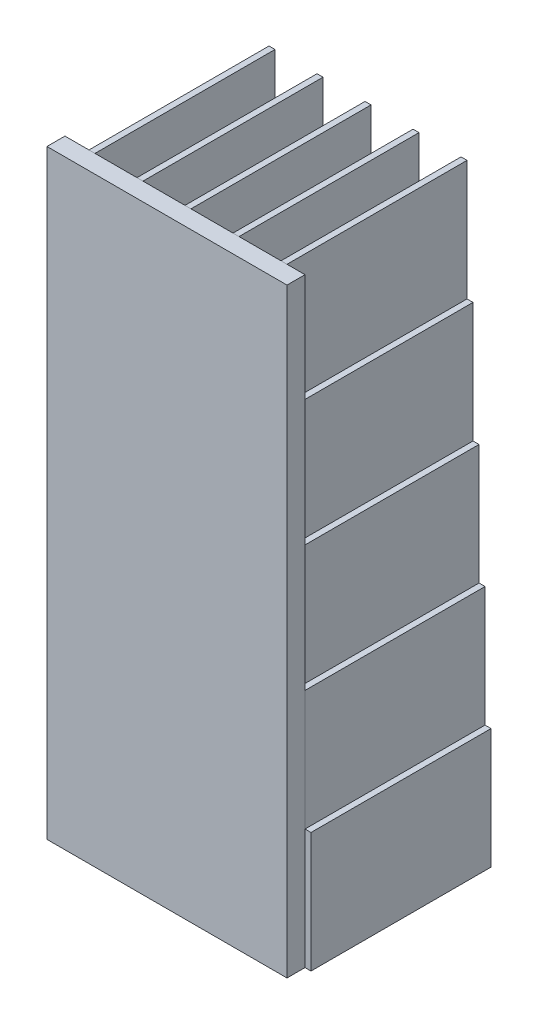
SolidWorks part; units mm, degrees
ref_plane "Front Plane" through (0, 0, 0) normal (0, 0, 1) x (1, 0, 0)
ref_plane "Top Plane" through (0, 0, 0) normal (0, 1, 0) x (1, 0, 0)
ref_plane "Right Plane" through (0, 0, 0) normal (1, 0, 0) x (0, 0, -1)
sketch "Sketch1" plane through (0, 0, 0) normal (0, 0, 1) x (1, 0, 0)
  line L361 (-45.534, 24.8846) -> (-44.534, 24.8846)
  line L362 (-46.534, 24.8846) -> (-45.534, 24.8846)
  line L363 (-46.534, 24.8846) -> (-46.534, 4.8846)
  line L364 (-46.534, 4.8846) -> (-45.534, 4.8846)
  line L365 (-45.534, 24.8846) -> (-45.534, 4.8846)
  line L366 (-45.534, 24.8846) -> (-44.534, 24.8846)
  line L367 (-45.534, 24.8846) -> (-45.534, 44.8846)
  line L368 (-45.534, 44.8846) -> (-44.534, 44.8846)
  line L369 (-44.534, 24.8846) -> (-44.534, 44.8846)
  line L371 (-44.534, 24.8846) -> (-44.534, 44.8846)
  line L372 (-44.534, 44.8846) -> (-43.534, 44.8846)
  line L374 (-38.534, 24.8846) -> (-37.534, 24.8846)
  line L379 (-38.534, 24.8846) -> (-38.534, 4.8846)
  line L384 (-38.534, 4.8846) -> (-37.534, 4.8846)
  line L389 (-37.534, 24.8846) -> (-37.534, 4.8846)
  line L392 (-40.534, 44.8846) -> (-39.534, 44.8846)
  line L393 (-39.534, 24.8846) -> (-39.534, 44.8846)
  line L394 (-37.534, 24.8846) -> (-36.534, 24.8846)
  line L395 (-39.534, 24.8846) -> (-38.534, 24.8846)
  line L396 (-39.534, 24.8846) -> (-39.534, 44.8846)
  line L397 (-39.534, 44.8846) -> (-38.534, 44.8846)
  line L398 (-38.534, 24.8846) -> (-38.534, 44.8846)
  line L399 (-45.534, 44.8846) -> (-44.534, 44.8846)
  line L400 (-45.534, 44.8846) -> (-44.534, 44.8846)
  line L403 (-44.534, 44.8846) -> (-44.534, 64.8846)
  line L404 (-44.534, 44.8846) -> (-43.534, 44.8846)
  line L405 (-44.534, 44.8846) -> (-44.534, 64.8846)
  line L406 (-44.534, 64.8846) -> (-43.534, 64.8846)
  line L407 (-43.534, 44.8846) -> (-43.534, 64.8846)
  line L408 (-44.534, 44.8846) -> (-43.534, 44.8846)
  line L410 (-43.534, 44.8846) -> (-43.534, 64.8846)
  line L411 (-43.534, 64.8846) -> (-42.534, 64.8846)
  line L413 (-37.534, 24.8846) -> (-36.534, 24.8846)
  line L418 (-37.534, 24.8846) -> (-37.534, 44.8846)
  line L421 (-41.534, 64.8846) -> (-40.534, 64.8846)
  line L422 (-40.534, 44.8846) -> (-40.534, 64.8846)
  line L423 (-37.534, 44.8846) -> (-36.534, 44.8846)
  line L424 (-40.534, 44.8846) -> (-39.534, 44.8846)
  line L425 (-40.534, 44.8846) -> (-40.534, 64.8846)
  line L426 (-40.534, 64.8846) -> (-39.534, 64.8846)
  line L427 (-39.534, 44.8846) -> (-39.534, 64.8846)
  line L428 (-40.534, 44.8846) -> (-39.534, 44.8846)
  line L429 (-39.534, 44.8846) -> (-38.534, 44.8846)
  line L430 (-39.534, 44.8846) -> (-39.534, 64.8846)
  line L433 (-36.534, 24.8846) -> (-36.534, 44.8846)
  line L438 (-44.534, 64.8846) -> (-43.534, 64.8846)
  line L441 (-43.534, 64.8846) -> (-43.534, 84.8846)
  line L442 (-44.534, 64.8846) -> (-43.534, 64.8846)
  line L443 (-43.534, 64.8846) -> (-42.534, 64.8846)
  line L444 (-43.534, 64.8846) -> (-43.534, 84.8846)
  line L445 (-43.534, 84.8846) -> (-42.534, 84.8846)
  line L446 (-42.534, 64.8846) -> (-42.534, 84.8846)
  line L447 (-43.534, 64.8846) -> (-42.534, 64.8846)
  line L449 (-42.534, 64.8846) -> (-42.534, 84.8846)
  line L450 (-42.534, 84.8846) -> (-41.534, 84.8846)
  line L451 (-41.534, 64.8846) -> (-41.534, 84.8846)
  line L452 (-36.534, 24.8846) -> (-36.534, 44.8846)
  line L453 (-41.534, 64.8846) -> (-40.534, 64.8846)
  line L454 (-41.534, 64.8846) -> (-41.534, 84.8846)
  line L455 (-41.534, 84.8846) -> (-40.534, 84.8846)
  line L456 (-40.534, 64.8846) -> (-40.534, 84.8846)
  line L457 (-41.534, 64.8846) -> (-40.534, 64.8846)
  line L458 (-40.534, 64.8846) -> (-39.534, 64.8846)
  line L459 (-40.534, 64.8846) -> (-40.534, 84.8846)
  line L462 (-40.534, 64.8846) -> (-39.534, 64.8846)
  line L467 (-36.534, 44.8846) -> (-35.534, 44.8846)
  line L476 (-32.534, 44.8846) -> (-31.534, 44.8846)
  line L477 (-43.534, 84.8846) -> (-42.534, 84.8846)
  line L480 (-42.534, 84.8846) -> (-42.534, 104.8846)
  line L481 (-43.534, 84.8846) -> (-42.534, 84.8846)
  line L482 (-42.534, 84.8846) -> (-41.534, 84.8846)
  line L483 (-42.534, 84.8846) -> (-42.534, 104.8846)
  line L484 (-42.534, 104.8846) -> (-41.534, 104.8846)
  line L485 (-41.534, 84.8846) -> (-41.534, 104.8846)
  line L486 (-42.534, 84.8846) -> (-41.534, 84.8846)
  line L487 (-41.534, 84.8846) -> (-40.534, 84.8846)
  line L488 (-41.534, 84.8846) -> (-41.534, 104.8846)
  line L491 (-41.534, 84.8846) -> (-40.534, 84.8846)
  line L496 (-31.534, 24.8846) -> (-31.534, 44.8846)
  line L501 (-44.534, 24.8846) -> (-43.534, 24.8846) [skipped]
  line L502 (-44.534, 24.8846) -> (-43.534, 24.8846) [skipped]
  line L503 (-43.534, 24.8846) -> (-43.534, 44.8846) [skipped]
  line L504 (-43.534, 24.8846) -> (-43.534, 44.8846) [skipped]
  line L505 (-42.534, 24.8846) -> (-42.534, 44.8846) [skipped]
  line L506 (-42.534, 24.8846) -> (-42.534, 44.8846) [skipped]
  line L507 (-41.534, 24.8846) -> (-41.534, 44.8846) [skipped]
  line L508 (-41.534, 24.8846) -> (-41.534, 44.8846) [skipped]
  line L509 (-40.534, 24.8846) -> (-40.534, 44.8846) [skipped]
  line L510 (-40.534, 24.8846) -> (-40.534, 44.8846) [skipped]
  line L511 (-40.534, 24.8846) -> (-39.534, 24.8846) [skipped]
  line L512 (-40.534, 24.8846) -> (-39.534, 24.8846) [skipped]
  line L513 (-41.534, 24.8846) -> (-40.534, 24.8846) [skipped]
  line L514 (-41.534, 24.8846) -> (-40.534, 24.8846) [skipped]
  line L515 (-42.534, 24.8846) -> (-41.534, 24.8846) [skipped]
  line L516 (-42.534, 24.8846) -> (-41.534, 24.8846) [skipped]
  line L517 (-43.534, 24.8846) -> (-42.534, 24.8846) [skipped]
  line L518 (-43.534, 24.8846) -> (-42.534, 24.8846) [skipped]
  line L519 (-43.534, 44.8846) -> (-42.534, 44.8846) [skipped]
  line L520 (-41.534, 44.8846) -> (-40.534, 44.8846) [skipped]
  line L521 (-42.534, 44.8846) -> (-41.534, 44.8846) [skipped]
  line L522 (-45.534, 44.8846) -> (-45.534, 64.8846) [skipped]
  line L523 (-38.534, 44.8846) -> (-38.534, 64.8846) [skipped]
  line L524 (-45.534, 64.8846) -> (-45.534, 84.8846) [skipped]
  line L525 (-44.534, 64.8846) -> (-44.534, 84.8846) [skipped]
  line L526 (-44.534, 64.8846) -> (-44.534, 84.8846) [skipped]
  line L527 (-45.534, 64.8846) -> (-44.534, 64.8846) [skipped]
  line L528 (-45.534, 64.8846) -> (-44.534, 64.8846) [skipped]
  line L529 (-45.534, 64.8846) -> (-44.534, 64.8846) [skipped]
  line L530 (-39.534, 64.8846) -> (-38.534, 64.8846) [skipped]
  line L531 (-39.534, 64.8846) -> (-38.534, 64.8846) [skipped]
  line L532 (-39.534, 64.8846) -> (-39.534, 84.8846) [skipped]
  line L533 (-39.534, 64.8846) -> (-39.534, 84.8846) [skipped]
  line L534 (-38.534, 64.8846) -> (-38.534, 84.8846) [skipped]
  line L535 (-45.534, 84.8846) -> (-45.534, 104.8846) [skipped]
  line L536 (-44.534, 84.8846) -> (-44.534, 104.8846) [skipped]
  line L537 (-44.534, 84.8846) -> (-44.534, 104.8846) [skipped]
  line L538 (-45.534, 84.8846) -> (-44.534, 84.8846) [skipped]
  line L539 (-45.534, 84.8846) -> (-44.534, 84.8846) [skipped]
  line L540 (-45.534, 84.8846) -> (-44.534, 84.8846) [skipped]
  line L541 (-44.534, 84.8846) -> (-43.534, 84.8846) [skipped]
  line L542 (-40.534, 84.8846) -> (-39.534, 84.8846) [skipped]
  line L543 (-39.534, 84.8846) -> (-39.534, 104.8846) [skipped]
  line L544 (-39.534, 84.8846) -> (-39.534, 104.8846) [skipped]
  line L545 (-39.534, 84.8846) -> (-38.534, 84.8846) [skipped]
  line L546 (-39.534, 84.8846) -> (-38.534, 84.8846) [skipped]
  line L547 (-38.534, 84.8846) -> (-38.534, 104.8846) [skipped]
  line L548 (-45.534, 104.8846) -> (-44.534, 104.8846) [skipped]
  line L549 (-44.534, 104.8846) -> (-43.534, 104.8846) [skipped]
  line L550 (-40.534, 104.8846) -> (-39.534, 104.8846) [skipped]
  line L551 (-39.534, 104.8846) -> (-38.534, 104.8846) [skipped]
  line L552 (-31.534, 24.8846) -> (-30.534, 24.8846)
  line L553 (-31.534, 24.8846) -> (-31.534, 44.8846)
  line L554 (-31.534, 44.8846) -> (-30.534, 44.8846)
  line L555 (-30.534, 24.8846) -> (-30.534, 44.8846)
  line L556 (-37.534, 44.8846) -> (-36.534, 44.8846)
  line L557 (-37.534, 44.8846) -> (-36.534, 44.8846)
  line L558 (-36.534, 44.8846) -> (-35.534, 44.8846)
  line L559 (-36.534, 44.8846) -> (-35.534, 44.8846)
  line L560 (-32.534, 44.8846) -> (-31.534, 44.8846)
  line L561 (-32.534, 44.8846) -> (-31.534, 44.8846)
  line L562 (-31.534, 44.8846) -> (-30.534, 44.8846)
  line L563 (-36.534, 44.8846) -> (-36.534, 64.8846)
  line L564 (-36.534, 44.8846) -> (-36.534, 64.8846)
  line L565 (-36.534, 64.8846) -> (-35.534, 64.8846)
  line L566 (-35.534, 44.8846) -> (-35.534, 64.8846)
  line L567 (-35.534, 44.8846) -> (-35.534, 64.8846)
  line L568 (-35.534, 64.8846) -> (-34.534, 64.8846)
  line L569 (-33.534, 64.8846) -> (-32.534, 64.8846)
  line L570 (-32.534, 44.8846) -> (-32.534, 64.8846)
  line L571 (-32.534, 44.8846) -> (-32.534, 64.8846)
  line L572 (-32.534, 64.8846) -> (-31.534, 64.8846)
  line L573 (-31.534, 44.8846) -> (-31.534, 64.8846)
  line L574 (-31.534, 44.8846) -> (-31.534, 64.8846)
  line L575 (-36.534, 64.8846) -> (-35.534, 64.8846)
  line L576 (-35.534, 64.8846) -> (-35.534, 84.8846)
  line L577 (-36.534, 64.8846) -> (-35.534, 64.8846)
  line L578 (-35.534, 64.8846) -> (-34.534, 64.8846)
  line L579 (-35.534, 64.8846) -> (-35.534, 84.8846)
  line L580 (-35.534, 84.8846) -> (-34.534, 84.8846)
  line L581 (-34.534, 64.8846) -> (-34.534, 84.8846)
  line L582 (-35.534, 64.8846) -> (-34.534, 64.8846)
  line L583 (-34.534, 64.8846) -> (-34.534, 84.8846)
  line L584 (-34.534, 84.8846) -> (-33.534, 84.8846)
  line L585 (-33.534, 64.8846) -> (-33.534, 84.8846)
  line L586 (-33.534, 64.8846) -> (-32.534, 64.8846)
  line L587 (-33.534, 64.8846) -> (-33.534, 84.8846)
  line L588 (-33.534, 84.8846) -> (-32.534, 84.8846)
  line L589 (-32.534, 64.8846) -> (-32.534, 84.8846)
  line L590 (-33.534, 64.8846) -> (-32.534, 64.8846)
  line L591 (-32.534, 64.8846) -> (-31.534, 64.8846)
  line L592 (-32.534, 64.8846) -> (-32.534, 84.8846)
  line L593 (-32.534, 64.8846) -> (-31.534, 64.8846)
  line L594 (-35.534, 84.8846) -> (-34.534, 84.8846)
  line L595 (-34.534, 84.8846) -> (-34.534, 104.8846)
  line L596 (-35.534, 84.8846) -> (-34.534, 84.8846)
  line L597 (-34.534, 84.8846) -> (-33.534, 84.8846)
  line L598 (-34.534, 84.8846) -> (-34.534, 104.8846)
  line L599 (-34.534, 104.8846) -> (-33.534, 104.8846)
  line L600 (-33.534, 84.8846) -> (-33.534, 104.8846)
  line L601 (-34.534, 84.8846) -> (-33.534, 84.8846)
  line L602 (-33.534, 84.8846) -> (-32.534, 84.8846)
  line L603 (-33.534, 84.8846) -> (-33.534, 104.8846)
  line L604 (-33.534, 84.8846) -> (-32.534, 84.8846)
  line L605 (-29.534, 24.8846) -> (-28.534, 24.8846)
  line L606 (-29.534, 24.8846) -> (-28.534, 24.8846)
  line L607 (-29.534, 24.8846) -> (-29.534, 44.8846)
  line L608 (-29.534, 44.8846) -> (-28.534, 44.8846)
  line L609 (-28.534, 24.8846) -> (-28.534, 44.8846)
  line L610 (-28.534, 24.8846) -> (-28.534, 44.8846)
  line L611 (-28.534, 44.8846) -> (-27.534, 44.8846)
  line L612 (-24.534, 44.8846) -> (-23.534, 44.8846)
  line L613 (-23.534, 24.8846) -> (-23.534, 44.8846)
  line L614 (-23.534, 24.8846) -> (-22.534, 24.8846)
  line L615 (-23.534, 24.8846) -> (-23.534, 44.8846)
  line L616 (-23.534, 44.8846) -> (-22.534, 44.8846)
  line L617 (-22.534, 24.8846) -> (-22.534, 44.8846)
  line L618 (-29.534, 44.8846) -> (-28.534, 44.8846)
  line L619 (-29.534, 44.8846) -> (-28.534, 44.8846)
  line L620 (-28.534, 44.8846) -> (-27.534, 44.8846)
  line L621 (-28.534, 44.8846) -> (-27.534, 44.8846)
  line L622 (-24.534, 44.8846) -> (-23.534, 44.8846)
  line L623 (-24.534, 44.8846) -> (-23.534, 44.8846)
  line L624 (-23.534, 44.8846) -> (-22.534, 44.8846)
  line L625 (-28.534, 44.8846) -> (-28.534, 64.8846)
  line L626 (-28.534, 44.8846) -> (-28.534, 64.8846)
  line L627 (-28.534, 64.8846) -> (-27.534, 64.8846)
  line L628 (-27.534, 44.8846) -> (-27.534, 64.8846)
  line L629 (-27.534, 44.8846) -> (-27.534, 64.8846)
  line L630 (-27.534, 64.8846) -> (-26.534, 64.8846)
  line L631 (-25.534, 64.8846) -> (-24.534, 64.8846)
  line L632 (-24.534, 44.8846) -> (-24.534, 64.8846)
  line L633 (-24.534, 44.8846) -> (-24.534, 64.8846)
  line L634 (-24.534, 64.8846) -> (-23.534, 64.8846)
  line L635 (-23.534, 44.8846) -> (-23.534, 64.8846)
  line L636 (-23.534, 44.8846) -> (-23.534, 64.8846)
  line L637 (-28.534, 64.8846) -> (-27.534, 64.8846)
  line L638 (-27.534, 64.8846) -> (-27.534, 84.8846)
  line L639 (-28.534, 64.8846) -> (-27.534, 64.8846)
  line L640 (-27.534, 64.8846) -> (-26.534, 64.8846)
  line L641 (-27.534, 64.8846) -> (-27.534, 84.8846)
  line L642 (-27.534, 84.8846) -> (-26.534, 84.8846)
  line L643 (-26.534, 64.8846) -> (-26.534, 84.8846)
  line L644 (-27.534, 64.8846) -> (-26.534, 64.8846)
  line L645 (-26.534, 64.8846) -> (-26.534, 84.8846)
  line L646 (-26.534, 84.8846) -> (-25.534, 84.8846)
  line L647 (-25.534, 64.8846) -> (-25.534, 84.8846)
  line L648 (-25.534, 64.8846) -> (-24.534, 64.8846)
  line L649 (-25.534, 64.8846) -> (-25.534, 84.8846)
  line L650 (-25.534, 84.8846) -> (-24.534, 84.8846)
  line L651 (-24.534, 64.8846) -> (-24.534, 84.8846)
  line L652 (-25.534, 64.8846) -> (-24.534, 64.8846)
  line L653 (-24.534, 64.8846) -> (-23.534, 64.8846)
  line L654 (-24.534, 64.8846) -> (-24.534, 84.8846)
  line L655 (-24.534, 64.8846) -> (-23.534, 64.8846)
  line L656 (-27.534, 84.8846) -> (-26.534, 84.8846)
  line L657 (-26.534, 84.8846) -> (-26.534, 104.8846)
  line L658 (-27.534, 84.8846) -> (-26.534, 84.8846)
  line L659 (-26.534, 84.8846) -> (-25.534, 84.8846)
  line L660 (-26.534, 84.8846) -> (-26.534, 104.8846)
  line L661 (-26.534, 104.8846) -> (-25.534, 104.8846)
  line L662 (-25.534, 84.8846) -> (-25.534, 104.8846)
  line L663 (-26.534, 84.8846) -> (-25.534, 84.8846)
  line L664 (-25.534, 84.8846) -> (-24.534, 84.8846)
  line L665 (-25.534, 84.8846) -> (-25.534, 104.8846)
  line L666 (-25.534, 84.8846) -> (-24.534, 84.8846)
  line L667 (-21.534, 24.8846) -> (-20.534, 24.8846)
  line L668 (-21.534, 24.8846) -> (-20.534, 24.8846)
  line L669 (-21.534, 24.8846) -> (-21.534, 44.8846)
  line L670 (-21.534, 44.8846) -> (-20.534, 44.8846)
  line L671 (-20.534, 24.8846) -> (-20.534, 44.8846)
  line L672 (-20.534, 24.8846) -> (-20.534, 44.8846)
  line L673 (-20.534, 44.8846) -> (-19.534, 44.8846)
  line L674 (-16.534, 44.8846) -> (-15.534, 44.8846)
  line L675 (-15.534, 24.8846) -> (-15.534, 44.8846)
  line L676 (-15.534, 24.8846) -> (-14.534, 24.8846)
  line L677 (-15.534, 24.8846) -> (-15.534, 44.8846)
  line L678 (-15.534, 44.8846) -> (-14.534, 44.8846)
  line L679 (-14.534, 24.8846) -> (-14.534, 44.8846)
  line L680 (-21.534, 44.8846) -> (-20.534, 44.8846)
  line L681 (-21.534, 44.8846) -> (-20.534, 44.8846)
  line L682 (-20.534, 44.8846) -> (-19.534, 44.8846)
  line L683 (-20.534, 44.8846) -> (-19.534, 44.8846)
  line L684 (-16.534, 44.8846) -> (-15.534, 44.8846)
  line L685 (-16.534, 44.8846) -> (-15.534, 44.8846)
  line L686 (-15.534, 44.8846) -> (-14.534, 44.8846)
  line L687 (-20.534, 44.8846) -> (-20.534, 64.8846)
  line L688 (-20.534, 44.8846) -> (-20.534, 64.8846)
  line L689 (-20.534, 64.8846) -> (-19.534, 64.8846)
  line L690 (-19.534, 44.8846) -> (-19.534, 64.8846)
  line L691 (-19.534, 44.8846) -> (-19.534, 64.8846)
  line L692 (-19.534, 64.8846) -> (-18.534, 64.8846)
  line L693 (-17.534, 64.8846) -> (-16.534, 64.8846)
  line L694 (-16.534, 44.8846) -> (-16.534, 64.8846)
  line L695 (-16.534, 44.8846) -> (-16.534, 64.8846)
  line L696 (-16.534, 64.8846) -> (-15.534, 64.8846)
  line L697 (-15.534, 44.8846) -> (-15.534, 64.8846)
  line L698 (-15.534, 44.8846) -> (-15.534, 64.8846)
  line L699 (-20.534, 64.8846) -> (-19.534, 64.8846)
  line L700 (-19.534, 64.8846) -> (-19.534, 84.8846)
  line L701 (-20.534, 64.8846) -> (-19.534, 64.8846)
  line L702 (-19.534, 64.8846) -> (-18.534, 64.8846)
  line L703 (-19.534, 64.8846) -> (-19.534, 84.8846)
  line L704 (-19.534, 84.8846) -> (-18.534, 84.8846)
  line L705 (-18.534, 64.8846) -> (-18.534, 84.8846)
  line L706 (-19.534, 64.8846) -> (-18.534, 64.8846)
  line L707 (-18.534, 64.8846) -> (-18.534, 84.8846)
  line L708 (-18.534, 84.8846) -> (-17.534, 84.8846)
  line L709 (-17.534, 64.8846) -> (-17.534, 84.8846)
  line L710 (-17.534, 64.8846) -> (-16.534, 64.8846)
  line L711 (-17.534, 64.8846) -> (-17.534, 84.8846)
  line L712 (-17.534, 84.8846) -> (-16.534, 84.8846)
  line L713 (-16.534, 64.8846) -> (-16.534, 84.8846)
  line L714 (-17.534, 64.8846) -> (-16.534, 64.8846)
  line L715 (-16.534, 64.8846) -> (-15.534, 64.8846)
  line L716 (-16.534, 64.8846) -> (-16.534, 84.8846)
  line L717 (-16.534, 64.8846) -> (-15.534, 64.8846)
  line L718 (-19.534, 84.8846) -> (-18.534, 84.8846)
  line L719 (-18.534, 84.8846) -> (-18.534, 104.8846)
  line L720 (-19.534, 84.8846) -> (-18.534, 84.8846)
  line L721 (-18.534, 84.8846) -> (-17.534, 84.8846)
  line L722 (-18.534, 84.8846) -> (-18.534, 104.8846)
  line L723 (-18.534, 104.8846) -> (-17.534, 104.8846)
  line L724 (-17.534, 84.8846) -> (-17.534, 104.8846)
  line L725 (-18.534, 84.8846) -> (-17.534, 84.8846)
  line L726 (-17.534, 84.8846) -> (-16.534, 84.8846)
  line L727 (-17.534, 84.8846) -> (-17.534, 104.8846)
  line L728 (-17.534, 84.8846) -> (-16.534, 84.8846)
  line L729 (-13.534, 24.8846) -> (-12.534, 24.8846)
  line L730 (-13.534, 24.8846) -> (-12.534, 24.8846)
  line L731 (-13.534, 24.8846) -> (-13.534, 44.8846)
  line L732 (-13.534, 44.8846) -> (-12.534, 44.8846)
  line L733 (-12.534, 24.8846) -> (-12.534, 44.8846)
  line L734 (-12.534, 24.8846) -> (-12.534, 44.8846)
  line L735 (-12.534, 44.8846) -> (-11.534, 44.8846)
  line L736 (-8.534, 44.8846) -> (-7.534, 44.8846)
  line L737 (-7.534, 24.8846) -> (-7.534, 44.8846)
  line L738 (-7.534, 24.8846) -> (-6.534, 24.8846)
  line L739 (-7.534, 24.8846) -> (-7.534, 44.8846)
  line L740 (-7.534, 44.8846) -> (-6.534, 44.8846)
  line L741 (-6.534, 24.8846) -> (-6.534, 44.8846)
  line L742 (-13.534, 44.8846) -> (-12.534, 44.8846)
  line L743 (-13.534, 44.8846) -> (-12.534, 44.8846)
  line L744 (-12.534, 44.8846) -> (-11.534, 44.8846)
  line L745 (-12.534, 44.8846) -> (-11.534, 44.8846)
  line L746 (-8.534, 44.8846) -> (-7.534, 44.8846)
  line L747 (-8.534, 44.8846) -> (-7.534, 44.8846)
  line L748 (-7.534, 44.8846) -> (-6.534, 44.8846)
  line L749 (-12.534, 44.8846) -> (-12.534, 64.8846)
  line L750 (-12.534, 44.8846) -> (-12.534, 64.8846)
  line L751 (-12.534, 64.8846) -> (-11.534, 64.8846)
  line L752 (-11.534, 44.8846) -> (-11.534, 64.8846)
  line L753 (-11.534, 44.8846) -> (-11.534, 64.8846)
  line L754 (-11.534, 64.8846) -> (-10.534, 64.8846)
  line L755 (-9.534, 64.8846) -> (-8.534, 64.8846)
  line L756 (-8.534, 44.8846) -> (-8.534, 64.8846)
  line L757 (-8.534, 44.8846) -> (-8.534, 64.8846)
  line L758 (-8.534, 64.8846) -> (-7.534, 64.8846)
  line L759 (-7.534, 44.8846) -> (-7.534, 64.8846)
  line L760 (-7.534, 44.8846) -> (-7.534, 64.8846)
  line L761 (-12.534, 64.8846) -> (-11.534, 64.8846)
  line L762 (-11.534, 64.8846) -> (-11.534, 84.8846)
  line L763 (-12.534, 64.8846) -> (-11.534, 64.8846)
  line L764 (-11.534, 64.8846) -> (-10.534, 64.8846)
  line L765 (-11.534, 64.8846) -> (-11.534, 84.8846)
  line L766 (-11.534, 84.8846) -> (-10.534, 84.8846)
  line L767 (-10.534, 64.8846) -> (-10.534, 84.8846)
  line L768 (-11.534, 64.8846) -> (-10.534, 64.8846)
  line L769 (-10.534, 64.8846) -> (-10.534, 84.8846)
  line L770 (-10.534, 84.8846) -> (-9.534, 84.8846)
  line L771 (-9.534, 64.8846) -> (-9.534, 84.8846)
  line L772 (-9.534, 64.8846) -> (-8.534, 64.8846)
  line L773 (-9.534, 64.8846) -> (-9.534, 84.8846)
  line L774 (-9.534, 84.8846) -> (-8.534, 84.8846)
  line L775 (-8.534, 64.8846) -> (-8.534, 84.8846)
  line L776 (-9.534, 64.8846) -> (-8.534, 64.8846)
  line L777 (-8.534, 64.8846) -> (-7.534, 64.8846)
  line L778 (-8.534, 64.8846) -> (-8.534, 84.8846)
  line L779 (-8.534, 64.8846) -> (-7.534, 64.8846)
  line L780 (-11.534, 84.8846) -> (-10.534, 84.8846)
  line L781 (-10.534, 84.8846) -> (-10.534, 104.8846)
  line L782 (-11.534, 84.8846) -> (-10.534, 84.8846)
  line L783 (-10.534, 84.8846) -> (-9.534, 84.8846)
  line L784 (-10.534, 84.8846) -> (-10.534, 104.8846)
  line L785 (-10.534, 104.8846) -> (-9.534, 104.8846)
  line L786 (-9.534, 84.8846) -> (-9.534, 104.8846)
  line L787 (-10.534, 84.8846) -> (-9.534, 84.8846)
  line L788 (-9.534, 84.8846) -> (-8.534, 84.8846)
  line L789 (-9.534, 84.8846) -> (-9.534, 104.8846)
  line L790 (-9.534, 84.8846) -> (-8.534, 84.8846)
  line L791 (-30.534, 24.8846) -> (-29.534, 24.8846)
  line L792 (-30.534, 24.8846) -> (-30.534, 4.8846)
  line L793 (-30.534, 4.8846) -> (-29.534, 4.8846)
  line L794 (-29.534, 24.8846) -> (-29.534, 4.8846)
  line L795 (-22.534, 24.8846) -> (-21.534, 24.8846)
  line L796 (-22.534, 24.8846) -> (-22.534, 4.8846)
  line L797 (-22.534, 4.8846) -> (-21.534, 4.8846)
  line L798 (-21.534, 24.8846) -> (-21.534, 4.8846)
  line L799 (-14.534, 24.8846) -> (-13.534, 24.8846)
  line L800 (-14.534, 24.8846) -> (-14.534, 4.8846)
  line L801 (-14.534, 4.8846) -> (-13.534, 4.8846)
  line L802 (-13.534, 24.8846) -> (-13.534, 4.8846)
  line L803 (-6.534, 24.8846) -> (-5.534, 24.8846)
  line L804 (-6.534, 24.8846) -> (-6.534, 4.8846)
  line L805 (-6.534, 4.8846) -> (-5.534, 4.8846)
  line L806 (-5.534, 24.8846) -> (-5.534, 4.8846)
  dimension "D1" = 7
  dimension "D2" = 4
  dimension "D5" = 2
extrude "Boss-Extrude1" add sketch "Sketch1" along normal blind 30 contours L365 L362 L363 L364 | L361 L369 L368 L367 | L395 L398 L397 L393 | L394 L433 L423 L418 | L389 L374 L379 L384 | L552 L555 L554 L496 | L605 L609 L608 L607 | L794 L791 L792 L793 | L614 L617 L616 L613 | L667 L671 L670 L669 | L798 L795 L796 L797 | L806 L803 L804 L805 | L802 L799 L800 L801 | L676 L679 L678 L675 | L729 L733 L732 L731 | L738 L741 L740 L737 | L372 L407 L406 L403 | L467 L566 L565 L563 | L476 L573 L572 L570 | L411 L446 L445 L441 | L421 L456 L455 L451 | L568 L581 L580 L576 | L569 L589 L588 L585 | L611 L628 L627 L625 | L630 L643 L642 L638 | L631 L651 L650 L647 | L612 L635 L634 L632 | L673 L690 L689 L687 | L692 L705 L704 L700 | L693 L713 L712 L709 | L674 L697 L696 L694 | L735 L752 L751 L749 | L754 L767 L766 L762 | L755 L775 L774 L771 | L736 L759 L758 L756 | L450 L485 L484 L480 | L584 L600 L599 L595 | L646 L662 L661 L657 | L708 L724 L723 L719 | L770 L786 L785 L781 | L427 L426 L425 L424
sketch "Sketch2" plane through (0, 0, 30) normal (0, 0, 1) x (1, 0, 0)
  line L1 (-46.534, 4.8846) -> (-6.534, 4.8846)
  line L2 (-46.534, 4.8846) -> (-46.534, 104.8846)
  line L3 (-46.534, 104.8846) -> (-6.534, 104.8846)
  line L4 (-6.534, 4.8846) -> (-6.534, 104.8846)
  dimension "D1" = 40
  dimension "D2" = 100
extrude "Boss-Extrude3" add sketch "Sketch2" along normal blind 3 separate body
